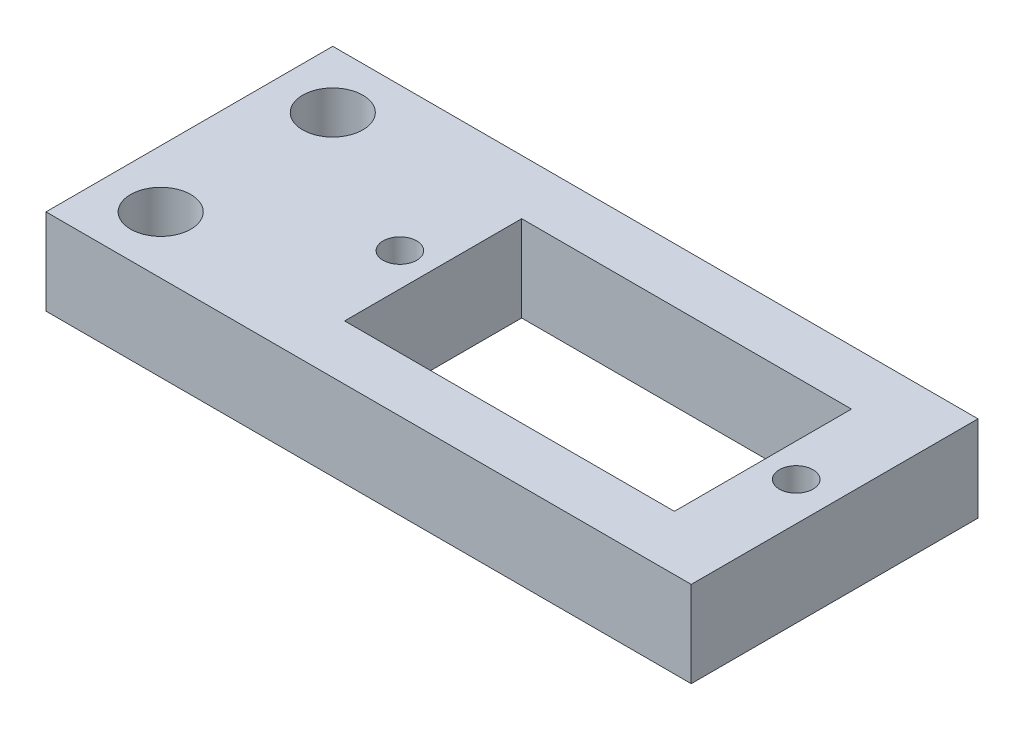
SolidWorks part; units mm, degrees
ref_plane "Front Plane" through (0, 0, 0) normal (0, 0, 1) x (1, 0, 0)
ref_plane "Top Plane" through (0, 0, 0) normal (0, 1, 0) x (1, 0, 0)
ref_plane "Right Plane" through (0, 0, 0) normal (1, 0, 0) x (0, 0, -1)
sketch "Sketch1" plane through (0, 0, 0) normal (0, 1, 0) x (1, 0, 0)
  line L1 (-22.5, -10) -> (22.5, -10)
  line L2 (-22.5, -10) -> (-22.5, 10)
  line L3 (-22.5, 10) -> (22.5, 10)
  line L4 (22.5, -10) -> (22.5, 10)
  line L5 (-22.5, -10) -> (22.5, 10) construction
  line L6 (-22.5, 10) -> (22.5, -10) construction
  point P0 (0, 0)
  dimension "D1" = 20
  dimension "D2" = 45
extrude "Boss-Extrude1" add sketch "Sketch1" along normal blind 6
sketch "Sketch2" plane through (0, 6, 0) normal (0, 1, 0) x (1, 0, 0)
  line L0 (-22.5, 10) -> (-22.5, -10) construction
  line L2 (-22.5, -10) -> (22.5, -10) construction
  line L3 (22.5, 10) -> (-22.5, 10) construction
  circle A0 centre (-18.5, -6) radius 2.1
  circle A1 centre (-18.5, 6) radius 2.1
  point P8 (-16.08, -10)
  dimension "D1" = 4.2
  dimension "D2" = 4.2
  dimension "D3" = 4
  dimension "D4" = 4
  dimension "D5" = 4
  dimension "D6" = 4
  dimension "D7" = 12
extrude "Cut-Extrude1" cut sketch "Sketch2" against normal blind 6
sketch "Sketch3" plane through (0, 6, 0) normal (0, 1, 0) x (1, 0, 0)
  line L0 (22.5, 10) -> (-22.5, 10) construction
  line L1 (-5.5, -6.175) -> (17.5, -6.175)
  line L2 (-5.5, -6.175) -> (-5.5, 6.175)
  line L3 (-5.5, 6.175) -> (17.5, 6.175)
  line L4 (17.5, -6.175) -> (17.5, 6.175)
  line L5 (22.5, -10) -> (22.5, 10) construction
  line L6 (6, -15.2525) -> (6, 16.1163) construction
  circle A0 centre (-7.82, 0) radius 1.175
  circle A1 centre (19.82, 0) radius 1.175
  dimension "D7" = 2.35
  dimension "D1" = 23
  dimension "D2" = 12.35
  dimension "D3" = 3.825
  dimension "D4" = 5
  dimension "D5" = 11.5
  dimension "D6" = 2.32
extrude "Cut-Extrude2" cut sketch "Sketch3" against normal blind 6
